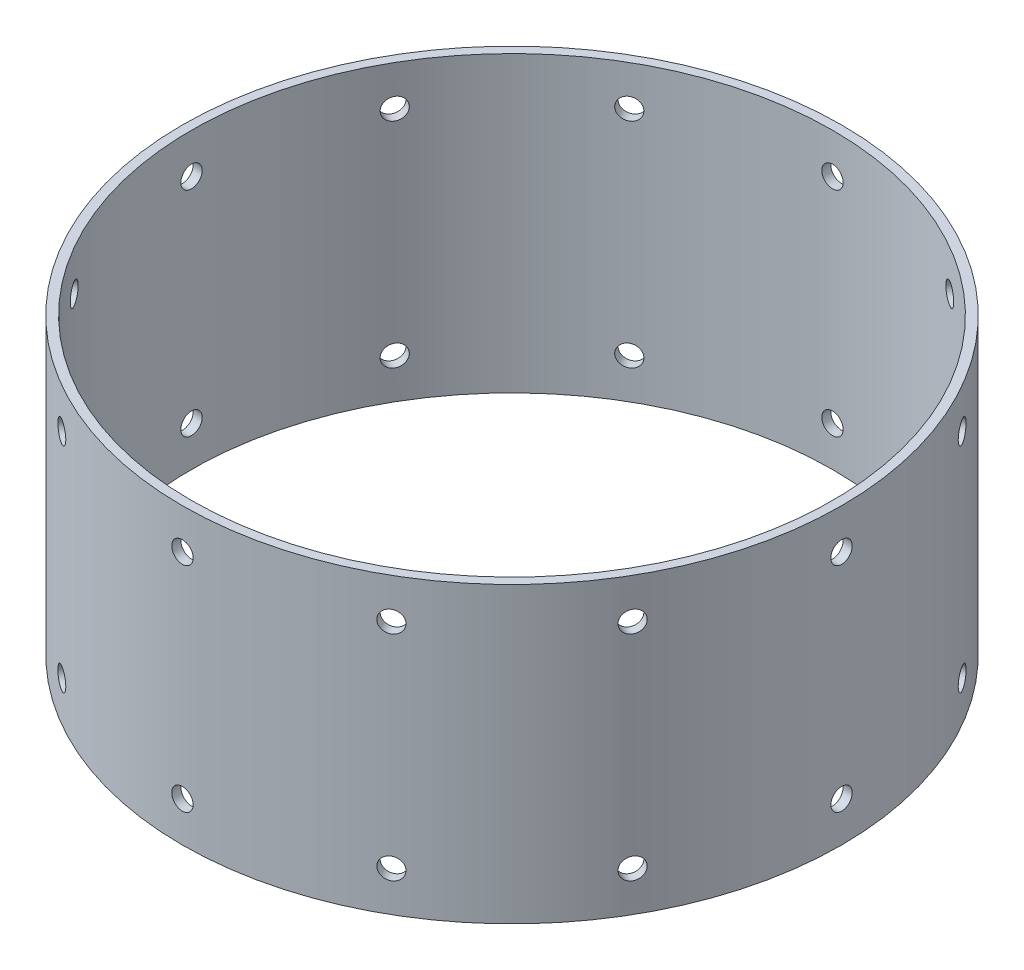
SolidWorks part; units mm, degrees
material "Fiberglass"
ref_plane "Front Plane" through (0, 0, 0) normal (0, 0, 1) x (1, 0, 0)
ref_plane "Top Plane" through (0, 0, 0) normal (0, 1, 0) x (1, 0, 0)
ref_plane "Right Plane" through (0, 0, 0) normal (1, 0, 0) x (0, 0, -1)
sketch "Sketch1" plane through (0, 0, 0) normal (0, 1, 0) x (1, 0, 0)
  circle A0 centre (0, 0) radius 76.2
  circle A1 centre (0, 0) radius 78.359
  dimension "D1" = 152.4
  dimension "D2" = 156.718
extrude "Boss-Extrude1" add sketch "Sketch1" along normal blind 69.85
sketch "Sketch2" plane through (0, 0, 0) normal (0, 0, 1) x (1, 0, 0)
  line L0 (0, 0) -> (0, 234.7266) construction
  line L1 (-76.2, 0) -> (76.2, 0) construction
  line L2 (-78.359, 0) -> (78.359, 0) construction
  line L3 (78.359, 34.925) -> (-54.7898, 34.925) construction
  line L4 (78.359, 0) -> (78.359, 69.85) construction
  circle A0 centre (0, 9.525) radius 2.54
  circle A1 centre (0, 60.325) radius 2.54
  dimension "D1" = 9.525
  dimension "D2" = 5.08
extrude "Cut-Extrude1" cut sketch "Sketch2" against normal through all
ref_axis "Axis1" through (0, 0, 0) along (0, 1, 0)
pattern_circular "CirPattern1" count 12 over 360 about axis through (0, 0, 0) along (0, 1, 0) of "Cut-Extrude1"
